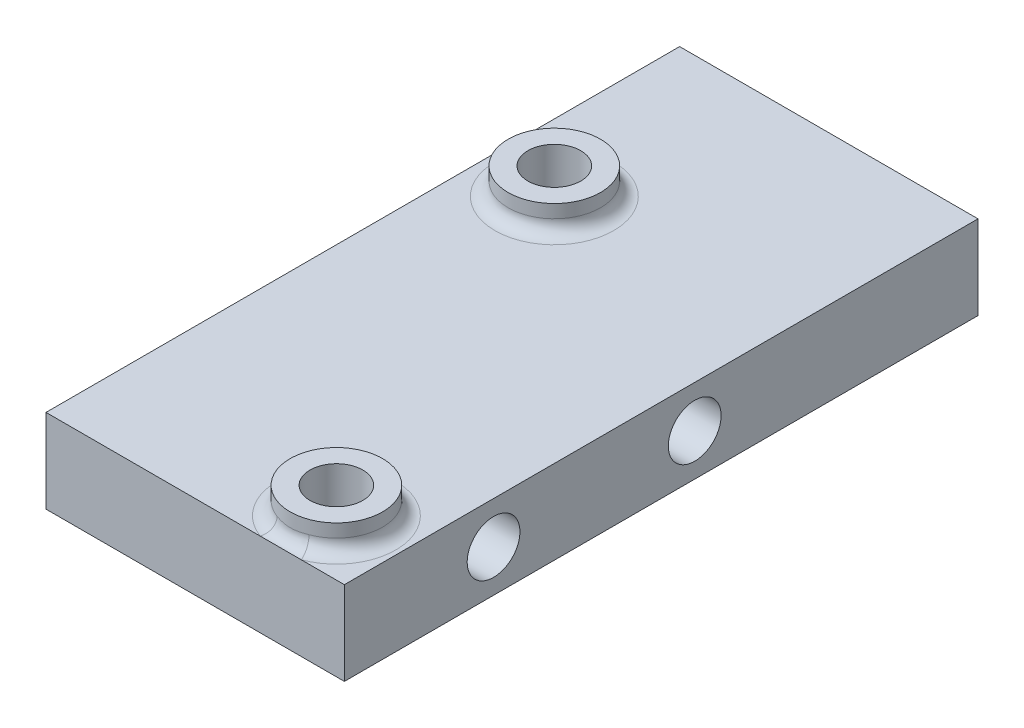
SolidWorks part; units mm, degrees
material "Nylon 12 (Density Only)"
ref_plane "Front Plane" through (0, 0, 0) normal (0, 0, 1) x (1, 0, 0)
ref_plane "Top Plane" through (0, 0, 0) normal (0, 1, 0) x (1, 0, 0)
ref_plane "Right Plane" through (0, 0, 0) normal (1, 0, 0) x (0, 0, -1)
sketch "Sketch1" plane through (0, 0, 0) normal (0, 1, 0) x (1, 0, 0)
  line L0 (0, 0) -> (22.86, 0)
  line L1 (0, 0) -> (0, 48.26)
  line L2 (22.86, 0) -> (22.86, 48.26)
  line L3 (0, 48.26) -> (22.86, 48.26)
  line L4 (0.127, 48.133) -> (22.733, 48.133)
  line L5 (22.733, 0.127) -> (22.733, 48.133)
  line L6 (0.127, 0.127) -> (22.733, 0.127)
  line L7 (0.127, 0.127) -> (0.127, 48.133)
  line L8 (11.43, 0.7937) -> (11.43, 0) construction
  line L9 (1.397, 0.7937) -> (21.463, 0.7938)
  line L10 (1.397, 0.7937) -> (1.397, 45.7518)
  line L11 (1.397, 45.7518) -> (21.463, 45.7518)
  line L12 (21.463, 0.7938) -> (21.463, 45.7518)
  circle A0 centre (5.207, 33.5598) radius 2
  circle A1 centre (17.907, 4.3498) radius 2
  dimension "D7" = 12.192
  dimension "D9" = 4
  dimension "D10" = 4
  dimension "D1" = 22.86
  dimension "D2" = 48.26
  dimension "D4" = 0.7937
  dimension "D5" = 20.066
  dimension "D6" = 44.958
  dimension "D8" = 3.81
  dimension "D11" = 3.556
  dimension "D12" = 3.556
  dimension "D3" = 0.127
extrude "Boss-Extrude1" add sketch "Sketch1" along normal blind 6.35
sketch "Sketch2" plane through (0.127, 0, 0) normal (-1, 0, 0) x (0, 0, 1)
  line L0 (-48.133, 0) -> (-0.127, 6.35) construction
  line L1 (-26.67, 3.175) -> (-24.13, 3.175) construction
  line L2 (-24.13, 3.175) -> (-11.43, 3.175) construction
  circle A0 centre (-26.67, 3.175) radius 2
  circle A1 centre (-11.43, 3.175) radius 2
  point P6 (-24.13, 3.175)
  dimension "D2" = 4
  dimension "D3" = 4
  dimension "D1" = 15.24
  dimension "D4" = 12.7
extrude "Cut-Extrude1" cut sketch "Sketch2" against normal through all contours A0 | A1
sketch "Sketch3" plane through (0, 6.35, 0) normal (0, 1, 0) x (1, 0, 0)
  circle A0 centre (17.907, 4.3498) radius 2 construction
  circle A1 centre (5.207, 33.5598) radius 2 construction
  circle A2 centre (17.907, 4.3498) radius 2
  circle A3 centre (5.207, 33.5598) radius 2
  circle A4 centre (5.207, 33.5598) radius 3.5
  circle A5 centre (17.907, 4.3498) radius 3.5
  dimension "D1" = 1.5
extrude "Boss-Extrude2" add sketch "Sketch3" along normal blind 2
fillet "Fillet1" radius 1 2 edges at (17.907, 6.35, -0.8497) (5.207, 6.35, -30.0597)
